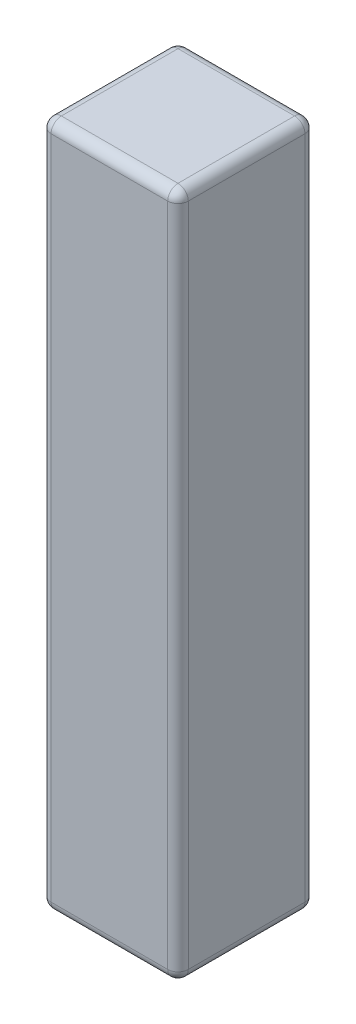
SolidWorks part; units mm, degrees
material "Alloy Steel"
ref_plane "Front" through (0, 0, 0) normal (0, 0, 1) x (1, 0, 0)
ref_plane "Top" through (0, 0, 0) normal (0, 1, 0) x (1, 0, 0)
ref_plane "Right" through (0, 0, 0) normal (1, 0, 0) x (0, 0, -1)
sketch "Sketch1" plane through (0, 0, 0) normal (0, 1, 0) x (1, 0, 0)
  line L0 (-1, 1) -> (1, -1) construction
  line L1 (-1, 1) -> (1, 1)
  line L2 (-1, 1) -> (-1, -1)
  line L3 (-1, -1) -> (1, -1)
  line L4 (1, 1) -> (1, -1)
  dimension "D1" = 2
extrude "Extrude2" add sketch "Sketch1" along normal mid plane 10
fillet "Fillet2" radius 0.15 12 edges at (0, 5, 1) (0, -5, 1) (1, 0, 1) (1, 5, 0) (1, -5, 0) (-1, 5, 0) (-1, 0, 1) (-1, -5, 0) (1, 0, -1) (0, 5, -1) (-1, 0, -1) (0, -5, -1)
